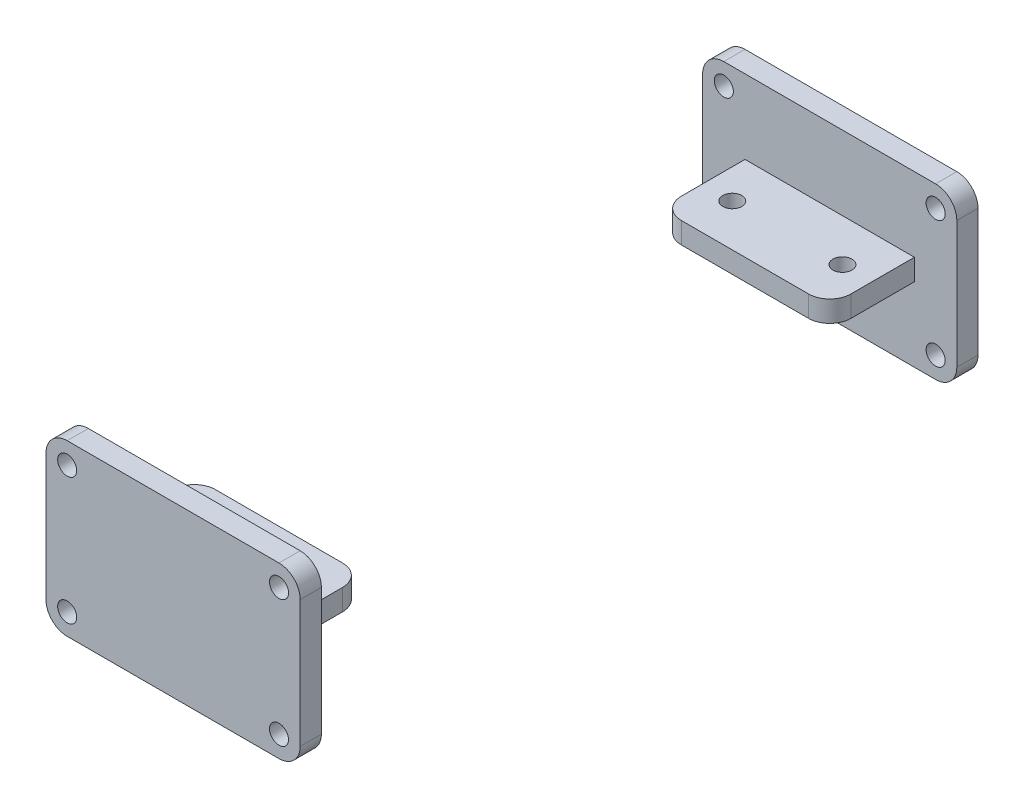
SolidWorks part; units mm, degrees
ref_plane "Front Plane" through (0, 0, 0) normal (0, 0, 1) x (1, 0, 0)
ref_plane "Top Plane" through (0, 0, 0) normal (0, 1, 0) x (1, 0, 0)
ref_plane "Right Plane" through (0, 0, 0) normal (1, 0, 0) x (0, 0, -1)
sketch "Sketch1" plane through (0, 0, 0) normal (0, 0, 1) x (1, 0, 0)
  line L1 (60, -40) -> (-60, -40)
  line L2 (60, -40) -> (60, 40)
  line L3 (60, 40) -> (-60, 40)
  line L4 (-60, -40) -> (-60, 40)
  line L5 (60, -40) -> (-60, 40) construction
  line L6 (60, 40) -> (-60, -40) construction
  point P0 (0, 0)
  dimension "D1" = 120
  dimension "D2" = 80
extrude "Boss-Extrude1" add sketch "Sketch1" along normal blind 10
fillet "Fillet1" radius 10 1 edges at (-60, 40, 5)
fillet "Fillet2" radius 10 1 edges at (60, -40, 5)
fillet "Fillet3" radius 10 1 edges at (-60, -40, 5)
fillet "Fillet4" radius 10 1 edges at (60, 40, 5)
sketch "Sketch3" plane through (0, 0, 0) normal (0, 0, 1) x (1, 0, 0)
  circle A1 centre (50, 30) radius 4.5
  circle A2 centre (50, -30) radius 4.5
  circle A3 centre (-50, -30) radius 4.5
  circle A4 centre (-50, 30) radius 4.5
extrude "Cut-Extrude2" cut sketch "Sketch3" along normal up to surface (10 mm away) up to face at (0, 0, 10)
sketch "Sketch5" plane through (0, 0, 0) normal (0, 0, 1) x (1, 0, 0)
  line L1 (40, -5) -> (-40, -5)
  line L2 (40, -5) -> (40, 5)
  line L3 (40, 5) -> (-40, 5)
  line L4 (-40, -5) -> (-40, 5)
  line L5 (40, -5) -> (-40, 5) construction
  line L6 (40, 5) -> (-40, -5) construction
  point P0 (0, 0)
  dimension "D1" = 80
  dimension "D2" = 10
extrude "Boss-Extrude2" add sketch "Sketch5" against normal blind 40
fillet "Fillet6" radius 10 1 edges at (-40, 0, -40)
fillet "Fillet7" radius 10 1 edges at (40, 0, -40)
sketch "Sketch6" plane through (0, 0, 0) normal (0, 1, 0) x (1, 0, 0)
  line L0 (30, 40) -> (-30, 40) construction
  line L1 (-40, 30) -> (-40, 0) construction
  line L2 (40, 30) -> (40, 0) construction
  line L3 (-40, 30) -> (-40, 0) construction
  circle A0 centre (-26, 20) radius 4.5
  circle A1 centre (26, 20) radius 4.5
  dimension "D1" = 20
  dimension "D3" = 14
  dimension "D5" = 9
  dimension "D6" = 9
  dimension "D2" = 14
  dimension "D4" = 20
extrude "Cut-Extrude3" cut sketch "Sketch6" along normal through all both and the other way through all
move or copy body "Body-Move/Copy2" bodies to move or copy 104 copy yes number of copies 1 rotation origin (0, 0, -150) rotation axis (1, 0, 0) rotation angle 180
